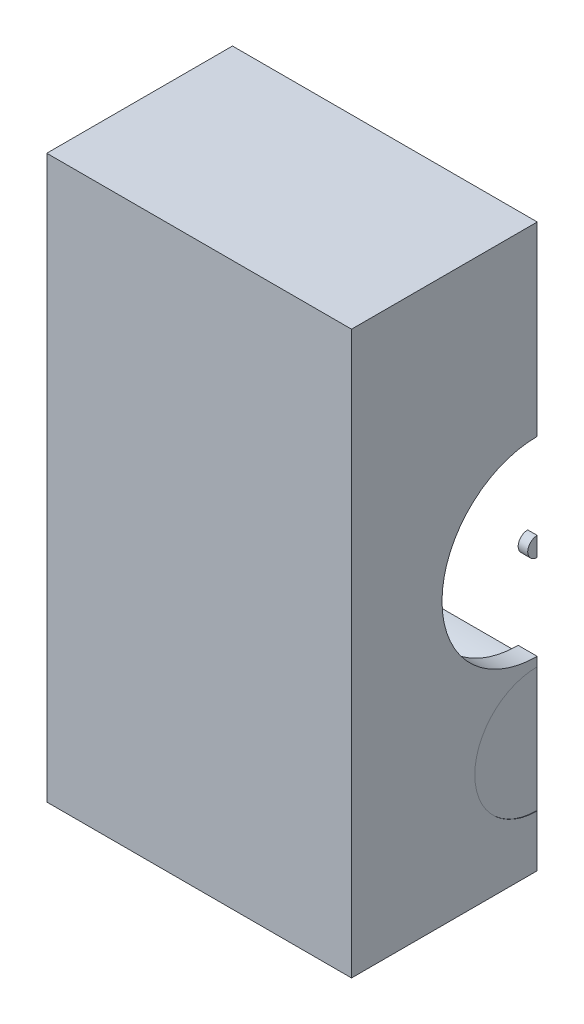
SolidWorks part; units mm, degrees
ref_plane "Plan de face" through (0, 0, 0) normal (0, 0, 1) x (1, 0, 0)
ref_plane "Plan de dessus" through (0, 0, 0) normal (0, 1, 0) x (1, 0, 0)
ref_plane "Plan de droite" through (0, 0, 0) normal (1, 0, 0) x (0, 0, -1)
sketch "Esquisse1" plane through (0, 0, 0) normal (0, 0, 1) x (1, 0, 0)
  line L0 (-20, 570) -> (300, 570)
  line L1 (0, 0) -> (280, 0)
  line L2 (0, 0) -> (0, 550)
  line L3 (0, 550) -> (280, 550)
  line L4 (280, 0) -> (280, 550)
  line L5 (300, -20) -> (300, 570)
  line L6 (-20, -20) -> (300, -20)
  line L7 (-20, -20) -> (-20, 570)
  dimension "D1" = 550
  dimension "D2" = 280
  dimension "D3" = 20
extrude "Boss.-Extru.1" add sketch "Esquisse1" along normal blind 390
sketch "Esquisse2" plane through (0, 0, 390) normal (0, 0, 1) x (1, 0, 0)
  line L1 (0, 550) -> (280, 550)
  line L2 (0, 550) -> (0, 0)
  line L3 (0, 0) -> (280, 0)
  line L4 (280, 550) -> (280, 0)
  dimension "D1" = 550
extrude "Boss.-Extru.2" add sketch "Esquisse2" against normal blind 20
sketch "Esquisse3" plane through (0, 0, 0) normal (0, 0, -1) x (-1, 0, 0)
  line L1 (-280, 550) -> (0, 550)
  line L2 (-280, 550) -> (-280, 0)
  line L3 (-280, 0) -> (0, 0)
  line L4 (0, 550) -> (0, 0)
extrude "Boss.-Extru.3" add sketch "Esquisse3" against normal blind 20
sketch "Esquisse4" plane through (300, 0, 0) normal (1, 0, 0) x (0, 0, -1)
  line L0 (-390, 570) -> (0, -20) construction
  line L1 (0, 570) -> (-390, -20) construction
  circle A0 centre (-195, 275) radius 100
  point P10 (-195, 275)
  dimension "D1" = 200
extrude "Enlèv. mat.-Extru.1" cut sketch "Esquisse4" against normal blind 20
sketch "Esquisse5" plane through (300, 0, 0) normal (1, 0, 0) x (0, 0, -1)
  line L0 (-195, 570) -> (-195, -20) construction
  line L1 (-390, 570) -> (0, 570) construction
  line L2 (-390, -20) -> (0, -20) construction
  line L3 (-390, 100) -> (0, 100) construction
  line L4 (-390, -20) -> (-390, 570) construction
  line L5 (0, -20) -> (0, 570) construction
  circle A0 centre (-195, 100) radius 65.55
  point P12 (-195, 100)
  dimension "D2" = 131.1
  dimension "D1" = 120
extrude "Enlèv. mat.-Extru.2" cut sketch "Esquisse5" against normal blind 20
sketch "Esquisse7" plane through (280, 0, 0) normal (-1, 0, 0) x (0, 0, 1)
  circle A0 centre (195, 100) radius 65.55
  circle A1 centre (195, 100) radius 68.55
  circle A2 centre (195, 100) radius 65.55 construction
  dimension "D1" = 3
  dimension "D2" = 0
extrude "Boss.-Extru.4" add sketch "Esquisse7" along normal blind 140
sketch "Esquisse8" plane through (300, 0, 0) normal (1, 0, 0) x (0, 0, -1)
  circle A0 centre (-195, 275) radius 10
  dimension "D1" = 20
extrude "Boss.-Extru.5" add sketch "Esquisse8" against normal blind 10 separate body
ref_plane "Plan1" through (299.5, 0, 0) normal (1, 0, 0) x (0, 0, -1)
sketch "Esquisse9" plane through (299.5, 0, 0) normal (1, 0, 0) x (0, 0, -1)
  circle A0 centre (-195, 100) radius 65.55 construction
  circle A1 centre (-195, 100) radius 65.55
  dimension "D1" = 0
extrude "Boss.-Extru.6" add sketch "Esquisse9" against normal blind 1
ref_plane "Plan2" through (140.5, 0, 0) normal (-1, 0, 0) x (0, 0, 1)
sketch "Esquisse10" plane through (140.5, 0, 0) normal (-1, 0, 0) x (0, 0, 1)
  circle A0 centre (195, 100) radius 65.55
  circle A1 centre (195, 100) radius 65.55 construction
  dimension "D1" = 0
extrude "Boss.-Extru.7" add sketch "Esquisse10" against normal blind 1
sketch "Esquisse11" plane through (300, 0, 0) normal (1, 0, 0) x (0, 0, -1)
  line L0 (-390, 570) -> (0, 570) construction
  line L1 (-195, 570) -> (0, 570)
  line L2 (-195, 570) -> (-195, -20)
  line L3 (-195, -20) -> (0, -20)
  line L4 (0, 570) -> (0, -20)
extrude "Enlèv. mat.-Extru.3" cut sketch "Esquisse11" against normal through all
